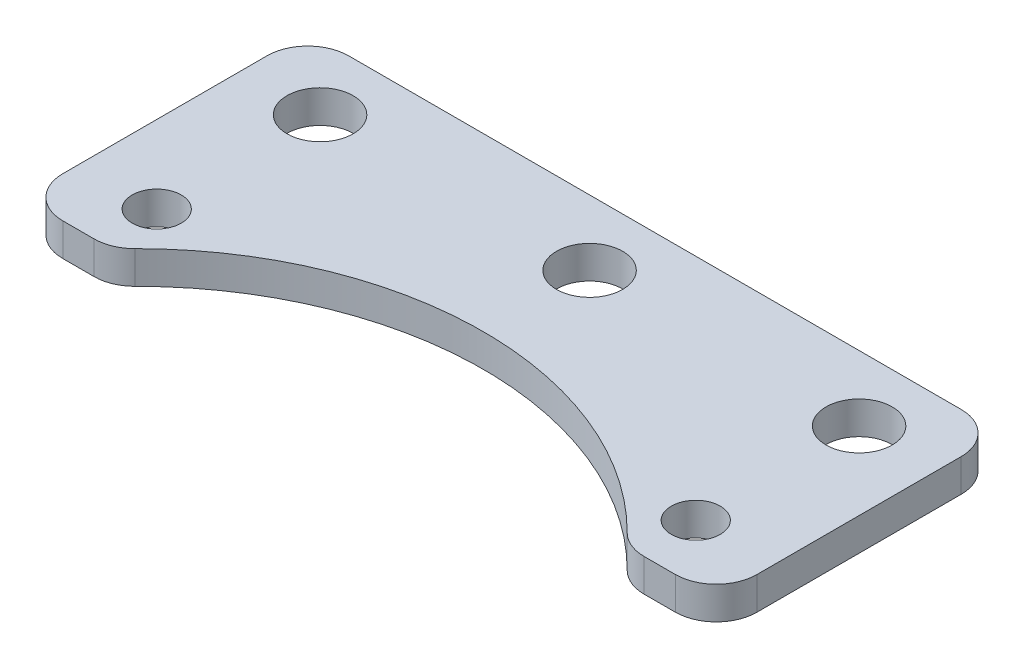
SolidWorks part; units mm, degrees
ref_plane "Front Plane" through (0, 0, 0) normal (0, 0, 1) x (1, 0, 0)
ref_plane "Top Plane" through (0, 0, 0) normal (0, 1, 0) x (1, 0, 0)
ref_plane "Right Plane" through (0, 0, 0) normal (1, 0, 0) x (0, 0, -1)
sketch "Sketch1" plane through (0, 0, 0) normal (0, 1, 0) x (1, 0, 0)
  line L0 (-33, -10.5) -> (-42.5, -10.5) construction
  line L1 (-42.5, -17.5) -> (42.5, -17.5)
  line L2 (-42.5, -17.5) -> (-42.5, 17.5)
  line L3 (-42.5, 17.5) -> (42.5, 17.5)
  line L4 (42.5, -17.5) -> (42.5, 17.5)
  line L5 (-42.5, -17.5) -> (42.5, 17.5) construction
  line L6 (-42.5, 17.5) -> (42.5, -17.5) construction
  line L7 (33, -10.5) -> (42.5, -10.5) construction
  circle A0 centre (-33, -10.5) radius 3
  circle A1 centre (33, -10.5) radius 3
  circle A2 centre (-33, 9.5) radius 4.05
  circle A3 centre (33, 9.5) radius 4.05
  circle A4 centre (0, 9.5) radius 4.05
  circle A5 centre (0, -46) radius 42.5
  point P0 (0, 0)
  point P16 (0, -3.5)
  point P19 (0, 0)
  point P20 (0, 0)
  point P21 (0, 0)
  point P22 (0, 0)
  point P23 (0, -5.4427)
  dimension "D1" = 6
  dimension "D2" = 6
  dimension "D3" = 66
  dimension "D5" = 7
  dimension "D6" = 8.1
  dimension "D7" = 8
  dimension "D9" = 85
  dimension "D4" = 85
  dimension "D8" = 20
  dimension "D10" = 7
extrude "Boss-Extrude1" add sketch "Sketch1" along normal blind 4 contours A5 L1 L4 L3 L2 A4 A3 A2 A1 A0
fillet "Fillet1" radius 5 6 edges at (42.5, 2, -17.5) (42.5, 2, 17.5) (31.5278, 2, 17.5) (-31.5278, 2, 17.5) (-42.5, 2, 17.5) (-42.5, 2, -17.5)
